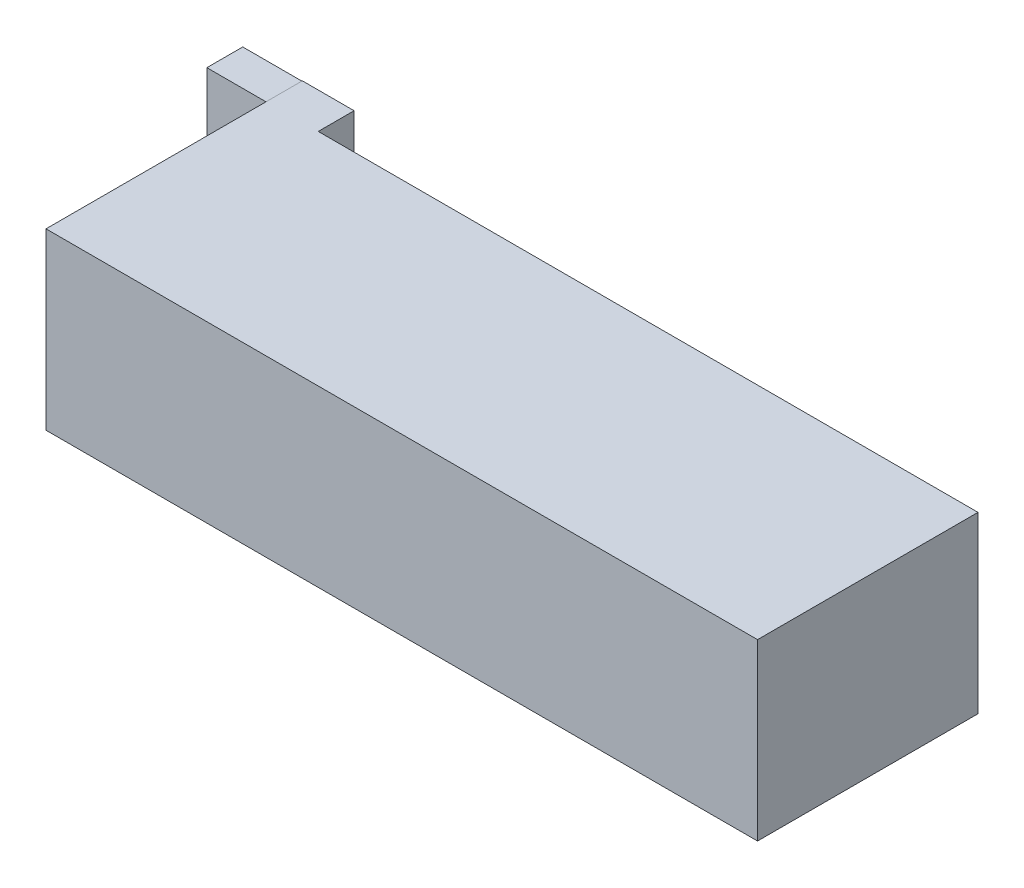
SolidWorks part; units mm, degrees
ref_plane "Front Plane" through (0, 0, 0) normal (0, 0, 1) x (1, 0, 0)
ref_plane "Top Plane" through (0, 0, 0) normal (0, 1, 0) x (1, 0, 0)
ref_plane "Right Plane" through (0, 0, 0) normal (1, 0, 0) x (0, 0, -1)
sketch "Sketch2" plane through (0, 0, 0) normal (0, 1, 0) x (1, 0, 0)
  line L1 (0, 0) -> (135.26, 0)
  line L2 (0, 0) -> (0, 41.91)
  line L3 (0, 41.91) -> (135.26, 41.91)
  line L4 (135.26, 0) -> (135.26, 41.91)
  dimension "D1" = 135.26
  dimension "D2" = 41.91
extrude "Boss-Extrude1" add sketch "Sketch2" along normal blind 33.16
sketch "Sketch3" plane through (0, 0, 0) normal (0, 1, 0) x (1, 0, 0)
  line L1 (0, 41.91) -> (9.84, 41.91)
  line L2 (0, 41.91) -> (0, 48.73)
  line L3 (0, 48.73) -> (9.84, 48.73)
  line L4 (9.84, 41.91) -> (9.84, 48.73)
  dimension "D1" = 9.84
  dimension "D2" = 6.82
extrude "Boss-Extrude2" add sketch "Sketch3" along normal blind 33.16
sketch "Sketch7" plane through (0, 0, -48.73) normal (0, 0, -1) x (-1, 0, 0)
  line L1 (0, 0) -> (11.33, 0)
  line L2 (0, 0) -> (0, 33.0723)
  line L3 (0, 33.0723) -> (11.33, 33.0723)
  line L4 (11.33, 0) -> (11.33, 33.0723)
  dimension "D1" = 33.0723
  dimension "D2" = 11.33
extrude "Boss-Extrude3" add sketch "Sketch7" against normal blind 6.82
